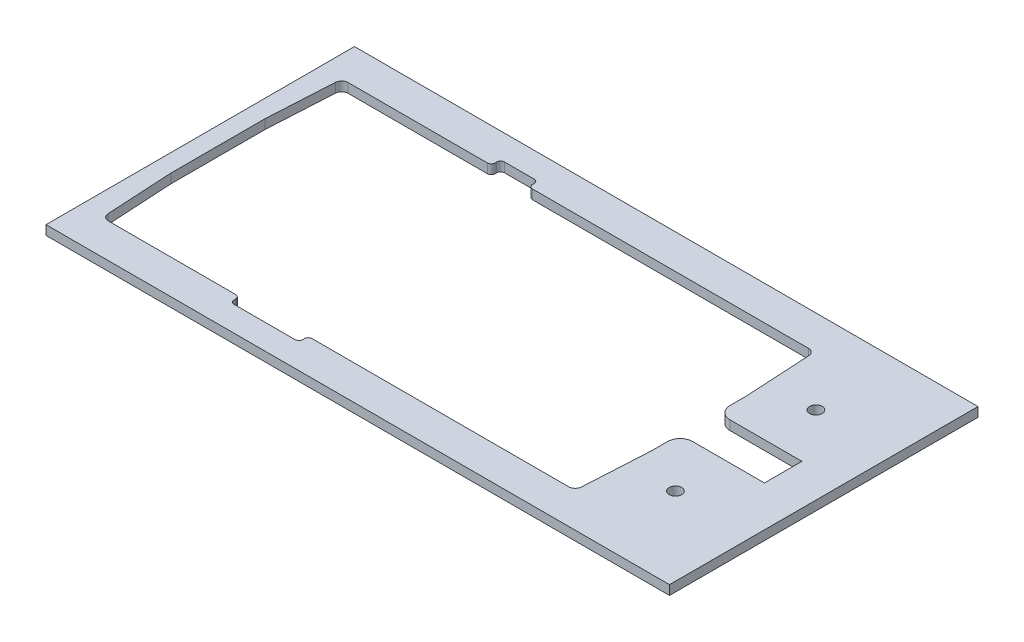
SolidWorks part; units mm, degrees
ref_plane "Front Plane" through (0, 0, 0) normal (0, 0, 1) x (1, 0, 0)
ref_plane "Top Plane" through (0, 0, 0) normal (0, 1, 0) x (1, 0, 0)
ref_plane "Right Plane" through (0, 0, 0) normal (1, 0, 0) x (0, 0, -1)
sketch "Sketch1" plane through (0, 0, 0) normal (0, 1, 0) x (1, 0, 0)
  line L0 (-41.1556, 15.8278) -> (3.3978, 15.8278)
  line L1 (-50.1422, 26.8278) -> (149.5478, 26.8278)
  line L2 (-50.1422, 26.8278) -> (-50.1422, -71.9722)
  line L3 (-50.1422, -71.9722) -> (149.5478, -71.9722)
  line L4 (149.5478, 26.8278) -> (149.5478, -71.9722)
  line L5 (109.5478, -7.4449) -> (109.5478, -12.5722)
  line L6 (113.5478, -16.5722) -> (136.5477, -16.5722)
  line L7 (136.5477, -16.5722) -> (136.5477, -28.5722)
  line L8 (136.5477, -28.5722) -> (113.5478, -28.5722)
  line L9 (109.5478, -32.5722) -> (109.5478, -37.6995)
  line L10 (106.2511, -60.9722) -> (24.0977, -60.9722)
  line L11 (-44.4522, -37.6995) -> (-44.4522, -7.4449)
  line L12 (4.6478, 17.0778) -> (4.6478, 17.5778)
  line L13 (5.8978, 18.8278) -> (15.3978, 18.8278)
  line L14 (16.6478, 17.5778) -> (16.6478, 17.0778)
  line L15 (17.8978, 15.8278) -> (106.2511, 15.8278)
  line L16 (0.8477, -62.2222) -> (0.8477, -62.7222)
  line L17 (2.0977, -63.9722) -> (21.5977, -63.9722)
  line L18 (22.8477, -62.7222) -> (22.8477, -62.2222)
  line L19 (-0.4023, -60.9722) -> (-41.1556, -60.9722)
  line L20 (-43.2522, 13.846) -> (-44.4522, -7.4449)
  line L21 (-44.4522, -37.6995) -> (-43.2522, -58.9904)
  line L22 (108.3478, 13.846) -> (109.5478, -7.4449)
  line L23 (109.5478, -37.6995) -> (108.3478, -58.9904)
  arc A0 (-41.1556, 15.8278) -> (-43.2522, 13.846) centre (-41.1556, 13.7278) ccw
  arc A1 (-43.2522, -58.9904) -> (-41.1556, -60.9722) centre (-41.1556, -58.8722) ccw
  arc A2 (108.3478, 13.846) -> (106.2511, 15.8278) centre (106.2511, 13.7278) ccw
  arc A3 (106.2511, -60.9722) -> (108.3478, -58.9904) centre (106.2511, -58.8722) ccw
  circle A4 centre (124.5478, -0.0722) radius 2
  circle A5 centre (124.5478, -45.0722) radius 2
  arc A6 (3.3978, 15.8278) -> (4.6478, 17.0778) centre (3.3978, 17.0778) ccw
  arc A7 (16.6478, 17.0778) -> (17.8978, 15.8278) centre (17.8978, 17.0778) ccw
  arc A8 (5.8978, 18.8278) -> (4.6478, 17.5778) centre (5.8978, 17.5778) ccw
  arc A9 (16.6478, 17.5778) -> (15.3978, 18.8278) centre (15.3978, 17.5778) ccw
  arc A10 (24.0977, -60.9722) -> (22.8477, -62.2222) centre (24.0977, -62.2222) ccw
  arc A11 (21.5977, -63.9722) -> (22.8477, -62.7222) centre (21.5977, -62.7222) ccw
  arc A12 (0.8477, -62.2222) -> (-0.4023, -60.9722) centre (-0.4023, -62.2222) ccw
  arc A13 (0.8477, -62.7222) -> (2.0977, -63.9722) centre (2.0977, -62.7222) ccw
  arc A14 (109.5478, -12.5722) -> (113.5478, -16.5722) centre (113.5478, -12.5722) ccw
  arc A15 (113.5478, -28.5722) -> (109.5478, -32.5722) centre (113.5478, -32.5722) ccw
  point P17 (22.8477, -62.4722)
  point P25 (136.5477, -22.5722)
  point P28 (-44.4522, -22.5722)
  dimension "D3" = 2.1
  dimension "D5" = 2.1
  dimension "D21" = 4.2
  dimension "D23" = 4.2
  dimension "D32" = 4
  dimension "D33" = 4
  dimension "D34" = 2.5
  dimension "D35" = 2.5
  dimension "D10" = 2.5
  dimension "D11" = 1.25
  dimension "D38" = 2.5
  dimension "D13" = 2.5
  dimension "D14" = 2.5
  dimension "D39" = 2.5
  dimension "D41" = 8
  dimension "D7" = 8
  dimension "D1" = 199.69
  dimension "D2" = 98.8
  dimension "D6" = 12
  dimension "D9" = 40
  dimension "D4" = 11
  dimension "D12" = 1.2
  dimension "D15" = 1.2
  dimension "D16" = 23.2727
  dimension "D17" = 23.2727
  dimension "D19" = 154
  dimension "D8" = 1.2
  dimension "D20" = 23.2727
  dimension "D22" = 76.8
  dimension "D24" = 1.2
  dimension "D25" = 23.2727
  dimension "D26" = 38.4
  dimension "D18" = 49.1
  dimension "D28" = 45
  dimension "D29" = 22.5
  dimension "D30" = 25
  dimension "D31" = 25
  dimension "D36" = 12
  dimension "D37" = 3
  dimension "D27" = 22
  dimension "D40" = 3
extrude "Boss-Extrude1" add sketch "Sketch1" along normal blind 3
equation "\"Fit\"= 1"
equation "\"cover width\"= 98.8"
equation "\"top phone insert length\"= 199.69"
equation "\"thinner acrylic\"= 3mm"
equation "\"D1@Sketch1\"=\"top phone insert length\""
equation "\"D2@Sketch1\"=\"cover width\""
equation "\"D1@Boss-Extrude1\"=\"thinner acrylic\""
equation "\"phone edge to bottom\"= 40"
equation "\"charge cable width\"= 12"
equation "\"charge cable length\"= 27"
equation "\"phone width\" = 76.8"
equation "\"phone length\"= 154"
equation "\"D6@Sketch1\"=\"charge cable width\""
equation "\"D9@Sketch1\"=\"phone edge to bottom\""
equation "\"button depth\"= 3"
equation "\"volume button length\"= 22"
equation "\"power button length\"= 12"
equation "\"power button from top\"= 49.1"
equation "\"volume button from top\"= 45.3"
equation "\"D4@Sketch1\"=(\"cover width\"-\"phone width\")/2"
equation "\"corner radius\"= 2.1"
equation "\"D3@Sketch1\"=\"corner radius\""
equation "\"D5@Sketch1\"=\"corner radius\""
equation "\"edge bend\"= 1.2"
equation "\"D12@Sketch1\"=\"edge bend\""
equation "\"D15@Sketch1\"=\"edge bend\""
equation "\"D16@Sketch1\" = \"phone width\" / 3.3"
equation "\"D17@Sketch1\" = \"phone width\" / 3.3"
equation "\"D19@Sketch1\"=\"phone length\""
equation "\"D21@Sketch1\"=\"corner radius\"*2"
equation "\"D8@Sketch1\"=\"edge bend\""
equation "\"D20@Sketch1\" = \"phone width\" / 3.3"
equation "\"D22@Sketch1\"=\"phone width\""
equation "\"D23@Sketch1\"=\"corner radius\"*2"
equation "\"D24@Sketch1\"=\"edge bend\""
equation "\"D25@Sketch1\" = \"phone width\" / 3.3"
equation "\"D26@Sketch1\"=\"phone width\"/2"
equation "\"D18@Sketch1\"=\"power button from top\""
equation "\"D29@Sketch1\"=\"D28@Sketch1\"/2"
equation "\"wire hole diameter\"=4"
equation "\"D32@Sketch1\"=\"wire hole diameter\""
equation "\"D33@Sketch1\"=\"wire hole diameter\""
equation "\"D36@Sketch1\"=\"power button length\""
equation "\"D37@Sketch1\"=\"button depth\""
equation "\"D27@Sketch1\"=\"volume button length\""
equation "\"D40@Sketch1\"=\"button depth\""
